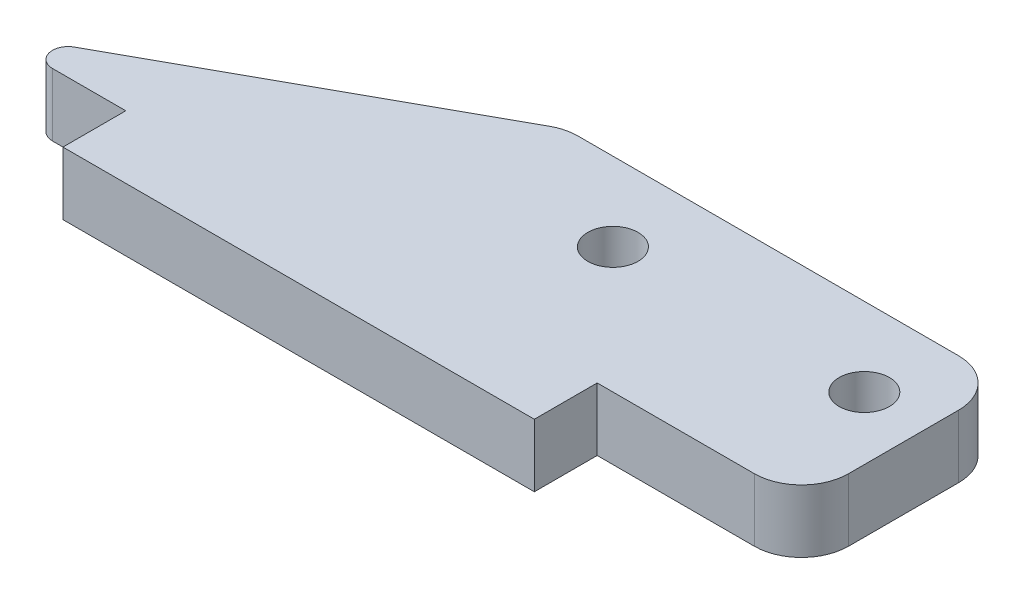
SolidWorks part; units mm, degrees
material "ﾊﾞﾙｻ"
ref_plane "正面" through (0, 0, 0) normal (0, 0, 1) x (1, 0, 0)
ref_plane "平面" through (0, 0, 0) normal (0, 1, 0) x (1, 0, 0)
ref_plane "右側面" through (0, 0, 0) normal (1, 0, 0) x (0, 0, -1)
sketch "ｽｹｯﾁ1" plane through (0, 0, 0) normal (0, 1, 0) x (1, 0, 0)
  line L0 (0, 0) -> (0, -4) construction
  line L1 (0, -4) -> (15, -4)
  line L2 (15, -4) -> (15, 0)
  line L3 (15, 0) -> (28, 0)
  line L4 (28, 0) -> (28, 13)
  line L5 (28, 13) -> (-23.5458, 13)
  line L6 (-23.5458, 13) -> (-23.5458, 0)
  line L7 (-23.5458, 0) -> (-15, 0)
  line L8 (-15, 0) -> (-15, -4)
  line L9 (-15, -4) -> (0, -4)
  line L10 (0, -3.465) -> (0, 13) construction
  line L11 (24, 8) -> (-0.4302, 8) construction
  line L12 (-23.5458, 0) -> (0, 13)
  circle A0 centre (8, 8) radius 1.6
  circle A1 centre (24, 8) radius 1.6
  dimension "D4" = 8
  dimension "D5" = 16
  dimension "D6" = 8
  dimension "D7" = 5
  dimension "D8" = 3.2
  dimension "D9" = 4
  dimension "D1" = 30
  dimension "D2" = 15
  dimension "D3" = 4
extrude "ﾎﾞｽ - 押し出し1" add sketch "ｽｹｯﾁ1" along normal blind 4 contours L12 L7 L8 L9 L1 L2 L3 L4 L5 A1 A0
fillet "ﾌｨﾚｯﾄ1" radius 3 3 edges at (28, 2, -13) (28, 2, 0) (0, 2, -13)
fillet "ﾌｨﾚｯﾄ2" radius 1 1 edges at (-23.5458, 2, 0)
